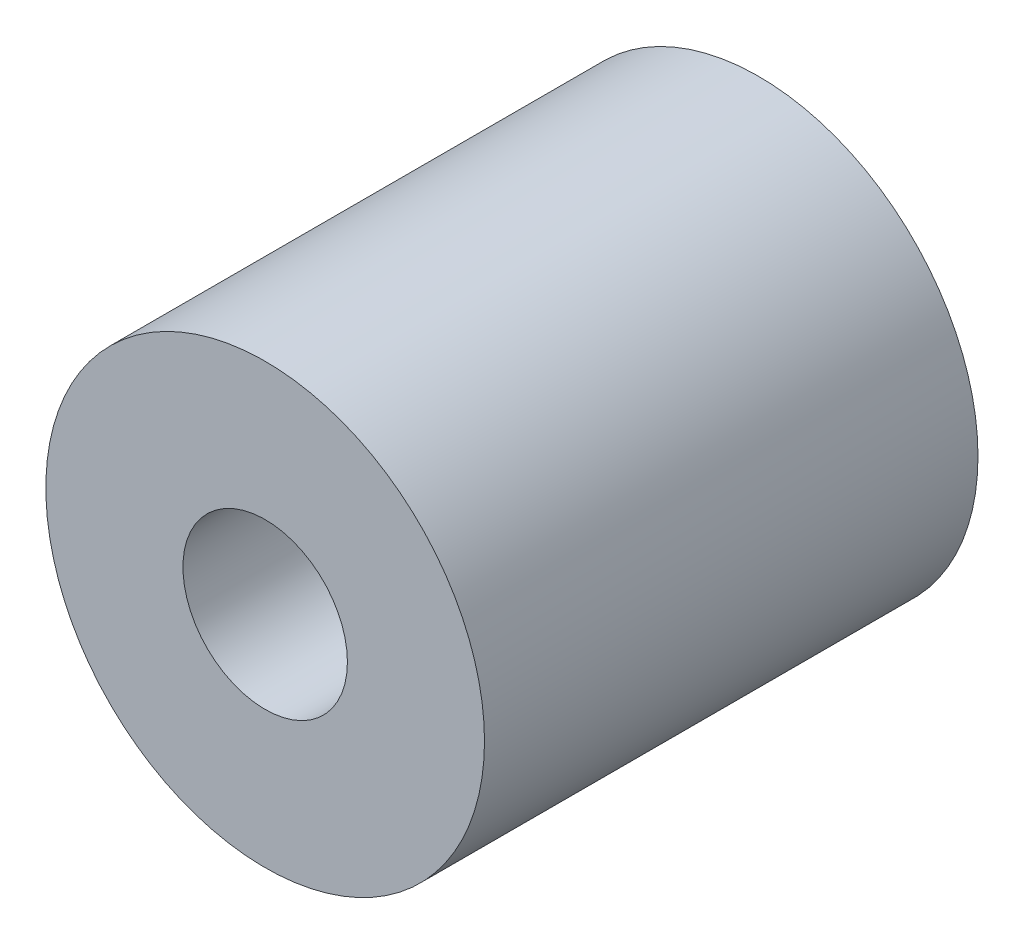
SolidWorks part; units mm, degrees
ref_plane "Front Plane" through (0, 0, 0) normal (0, 0, 1) x (1, 0, 0)
ref_plane "Top Plane" through (0, 0, 0) normal (0, 1, 0) x (1, 0, 0)
ref_plane "Right Plane" through (0, 0, 0) normal (1, 0, 0) x (0, 0, -1)
sketch "Sketch1" plane through (0, 0, 0) normal (0, 0, 1) x (1, 0, 0)
  circle A0 centre (0, 0) radius 15
  circle A1 centre (0, 0) radius 40
  dimension "D1" = 30
  dimension "D2" = 80
extrude "Boss-Extrude1" add sketch "Sketch1" along normal blind 90
